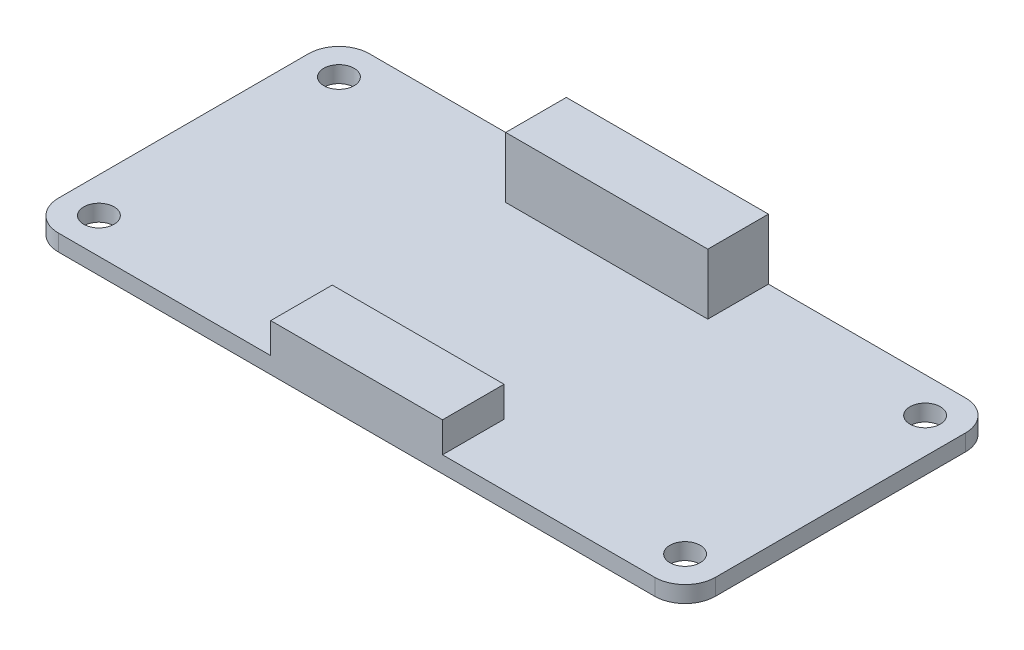
SolidWorks part; units mm, degrees
ref_plane "前视基准面" through (0, 0, 0) normal (0, 0, 1) x (1, 0, 0)
ref_plane "上视基准面" through (0, 0, 0) normal (0, 1, 0) x (1, 0, 0)
ref_plane "右视基准面" through (0, 0, 0) normal (1, 0, 0) x (0, 0, -1)
sketch "草图1" plane through (0, 0, 0) normal (0, 1, 0) x (1, 0, 0)
  line L1 (-29.5, 15.375) -> (29.5, 15.375)
  line L2 (-32.5, 12.375) -> (-32.5, -12.375)
  line L3 (-29.5, -15.375) -> (29.5, -15.375)
  line L4 (32.5, 12.375) -> (32.5, -12.375)
  line L5 (-32.5, 15.375) -> (32.5, -15.375) construction
  line L6 (-32.5, -15.375) -> (32.5, 15.375) construction
  arc A0 (-32.5, -12.375) -> (-29.5, -15.375) centre (-29.5, -12.375) ccw
  arc A1 (29.5, -15.375) -> (32.5, -12.375) centre (29.5, -12.375) ccw
  arc A2 (29.5, 15.375) -> (32.5, 12.375) centre (29.5, 12.375) cw
  arc A3 (-29.5, 15.375) -> (-32.5, 12.375) centre (-29.5, 12.375) ccw
  point P0 (0, 0)
  dimension "D3" = 3
  dimension "D1" = 30.75
  dimension "D2" = 65
extrude "凸台-拉伸1" add sketch "草图1" along normal blind 1.63
sketch "草图2" plane through (0, 1.63, 0) normal (0, 1, 0) x (1, 0, 0)
  line L0 (29.5, 15.375) -> (-29.5, 15.375) construction
  line L2 (-32.5, 12.375) -> (-32.5, -12.375) construction
  line L3 (-29.5, -15.375) -> (29.5, -15.375) construction
  line L4 (32.5, -12.375) -> (32.5, 12.375) construction
  circle A0 centre (-29, 11.875) radius 1.5
  circle A1 centre (-29, -11.875) radius 1.5
  circle A2 centre (29, -11.875) radius 1.5
  circle A3 centre (29, 11.875) radius 1.5
  dimension "D1" = 3
  dimension "D2" = 3.5
  dimension "D3" = 3.5
  dimension "D4" = 3.5
  dimension "D5" = 3.5
extrude "切除-拉伸1" cut sketch "草图2" against normal through all
sketch "草图8" plane through (0, 0, 0) normal (0, -1, 0) x (1, 0, 0)
  line L0 (29.5, -15.375) -> (-29.5, -15.375) construction
  line L1 (-25.7, -8.735) -> (25.3, -8.735)
  line L2 (-25.7, -8.735) -> (-25.7, -13.735)
  line L3 (-25.7, -13.735) -> (25.3, -13.735)
  line L4 (25.3, -8.735) -> (25.3, -13.735)
  line L5 (32.5, 12.375) -> (32.5, -12.375) construction
  dimension "D1" = 5
  dimension "D2" = 51
  dimension "D3" = 1.64
  dimension "D4" = 7.2
extrude "凸台-拉伸6" add sketch "草图8" along normal blind 3.68
sketch "草图9" plane through (0, 1.63, 0) normal (0, 1, 0) x (1, 0, 0)
  line L0 (-29.5, -15.375) -> (29.5, -15.375) construction
  line L1 (-8.5, -15.375) -> (8.5, -15.375)
  line L2 (-8.5, -15.375) -> (-8.5, -9.2845)
  line L3 (-8.5, -9.2845) -> (8.5, -9.2845)
  line L4 (8.5, -15.375) -> (8.5, -9.2845)
  line L5 (32.5, -12.375) -> (32.5, 12.375) construction
  line L6 (-32.5, 12.375) -> (-32.5, -12.375) construction
  dimension "D1" = 24
  dimension "D2" = 24
extrude "凸台-拉伸7" add sketch "草图9" along normal blind 3
sketch "草图10" plane through (0, 1.63, 0) normal (0, 1, 0) x (1, 0, 0)
  line L0 (29.5, 15.375) -> (-29.5, 15.375) construction
  line L1 (-10, 15.375) -> (10, 15.375)
  line L2 (-10, 15.375) -> (-10, 9.375)
  line L3 (-10, 9.375) -> (10, 9.375)
  line L4 (10, 15.375) -> (10, 9.375)
  line L5 (8.5, -9.2845) -> (-8.5, -9.2845) construction
  point P6 (0, 15.375)
  point P9 (0, -9.2845)
  dimension "D1" = 6
  dimension "D2" = 20
extrude "凸台-拉伸8" add sketch "草图10" along normal blind 6
